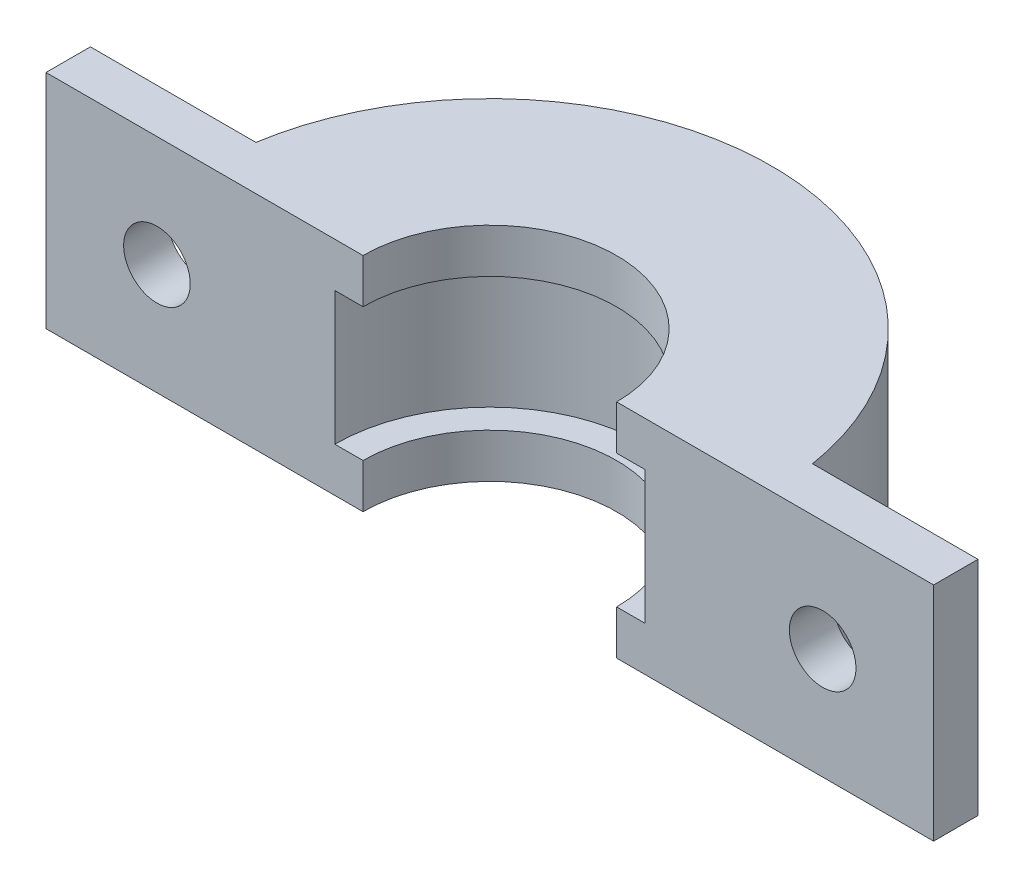
SolidWorks part; units mm, degrees
ref_plane "Front Plane" through (0, 0, 0) normal (0, 0, 1) x (1, 0, 0)
ref_plane "Top Plane" through (0, 0, 0) normal (0, 1, 0) x (1, 0, 0)
ref_plane "Right Plane" through (0, 0, 0) normal (1, 0, 0) x (0, 0, -1)
sketch "Sketch1" plane through (0, 0, 0) normal (0, 1, 0) x (1, 0, 0)
  line L0 (12.7, 0) -> (-12.7, 0)
  circle A0 centre (0, 0) radius 12.7
  circle A1 centre (0, 0) radius 5.715
  point P7 (0, 0)
  dimension "D1" = 25.4
  dimension "D2" = 11.43
extrude "Boss-Extrude1" add sketch "Sketch1" along normal mid plane 10 contours A1 L0 A0
ref_plane "Plane1" through (0, 0, 0) normal (0, 1, 0) x (1, 0, 0)
sketch "Sketch2" plane through (0, 0, 0) normal (0, 1, 0) x (1, 0, 0)
  line L0 (-6.985, 0) -> (6.985, 0)
  circle A0 centre (0, 0) radius 6.985
  dimension "D1" = 13.97
extrude "Cut-Extrude1" cut sketch "Sketch2" against normal mid plane 6 contours L0 A0
sketch "Sketch3" plane through (0, 0, 0) normal (0, 0, 1) x (1, 0, 0)
  line L0 (0, -5) -> (0, 5) construction
  line L1 (11, 5) -> (20, 5)
  line L2 (5.715, 5) -> (-5.715, 5) construction
  line L3 (6.985, 0) -> (-6.985, 0) construction
  line L4 (-11, -5) -> (-20, -5)
  line L5 (-11, -5) -> (-11, 5)
  line L6 (-11, 5) -> (-20, 5)
  line L7 (-20, -5) -> (-20, 5)
  line L8 (-11, -5) -> (-20, 5) construction
  line L9 (-11, 5) -> (-20, -5) construction
  line L10 (20, -5) -> (20, 5)
  line L11 (-5.715, -5) -> (-12.7, -5) construction
  line L12 (11, -5) -> (20, -5)
  line L13 (-12.7, 5) -> (-12.7, -5) construction
  line L18 (11, -5) -> (11, 5)
  circle A2 centre (-15, 0) radius 1.5
  circle A3 centre (15, 0) radius 1.5
  point P0 (-15.5, 0)
  point P4 (0, 0)
  dimension "D2" = 5
  dimension "D4" = 3
  dimension "D1" = 9
  dimension "D3" = 1.7
extrude "Boss-Extrude2" add sketch "Sketch3" against normal blind 2
